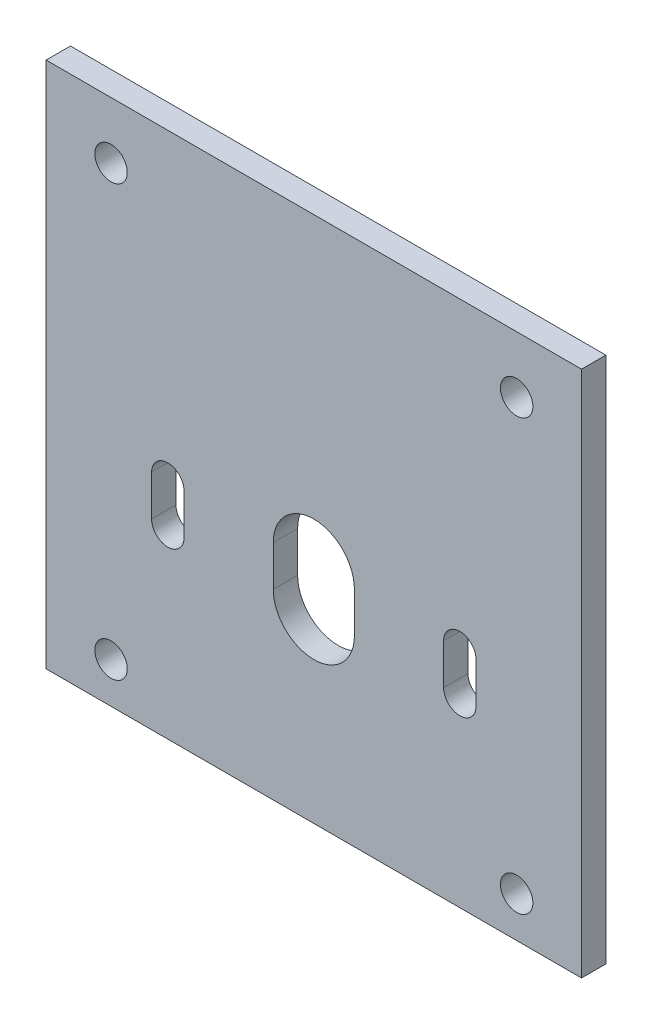
SolidWorks part; units mm, degrees
ref_plane "Front Plane" through (0, 0, 0) normal (0, 0, 1) x (1, 0, 0)
ref_plane "Top Plane" through (0, 0, 0) normal (0, 1, 0) x (1, 0, 0)
ref_plane "Right Plane" through (0, 0, 0) normal (1, 0, 0) x (0, 0, -1)
sketch "Sketch1" plane through (0, 0, 0) normal (1, 0, 0) x (0, 0, -1)
  line L0 (0, 0) -> (0, -65)
  line L1 (0, -65) -> (-3, -65)
  line L2 (-3, -65) -> (-3, 0)
  line L3 (-3, 0) -> (0, 0)
  dimension "D1" = 65
  dimension "D2" = 3
extrude "Boss-Extrude1" add sketch "Sketch1" against normal blind 66
sketch "Sketch5" plane through (0, 0, 0) normal (0, 0, -1) x (-1, 0, 0)
  line L0 (33, -65) -> (33, 0) construction
  line L1 (66, -65) -> (0, -65) construction
  line L2 (66, 0) -> (0, 0) construction
  line L3 (0, -32.5) -> (66, -32.5) construction
  line L4 (0, -65) -> (0, 0) construction
  line L5 (66, -65) -> (66, 0) construction
  line L6 (66, -37.5) -> (0, -37.5) construction
  line L7 (33, -37.5) -> (33, -42.5) construction
  line L8 (38, -37.5) -> (38, -42.5)
  line L9 (28, -37.5) -> (28, -42.5)
  line L10 (15, -37.5) -> (15, -42.5) construction
  line L11 (17, -37.5) -> (17, -42.5)
  line L12 (13, -37.5) -> (13, -42.5)
  line L13 (51, -37.5) -> (51, -42.5) construction
  line L14 (53, -37.5) -> (53, -42.5)
  line L15 (49, -37.5) -> (49, -42.5)
  circle A1 centre (8, -7) radius 2
  circle A2 centre (58, -7) radius 2
  arc A5 (38, -37.5) -> (28, -37.5) centre (33, -37.5) ccw
  arc A6 (28, -42.5) -> (38, -42.5) centre (33, -42.5) ccw
  arc A7 (17, -37.5) -> (13, -37.5) centre (15, -37.5) ccw
  arc A8 (13, -42.5) -> (17, -42.5) centre (15, -42.5) ccw
  arc A9 (53, -37.5) -> (49, -37.5) centre (51, -37.5) ccw
  arc A10 (49, -42.5) -> (53, -42.5) centre (51, -42.5) ccw
  circle A11 centre (8, -60) radius 2
  circle A12 centre (58, -60) radius 2
  point P22 (15, -40)
  point P24 (33, -40)
  point P34 (51, -40)
  dimension "D2" = 5
  dimension "D7" = 5
  dimension "D8" = 18
  dimension "D12" = 4
  dimension "D13" = 4
  dimension "D18" = 4
  dimension "D19" = 4
  dimension "D20" = 2
  dimension "D21" = 2
  dimension "D22" = 2
  dimension "D23" = 2
  dimension "D24" = 5
  dimension "D1" = 10
  dimension "D3" = 8
  dimension "D4" = 8
  dimension "D5" = 7
  dimension "D6" = 7
  dimension "D9" = 5
  dimension "D10" = 18
  dimension "D11" = 5
  dimension "D14" = 5
  dimension "D15" = 5
  dimension "D16" = 8
  dimension "D17" = 8
extrude "Cut-Extrude3" cut sketch "Sketch5" against normal up to next
